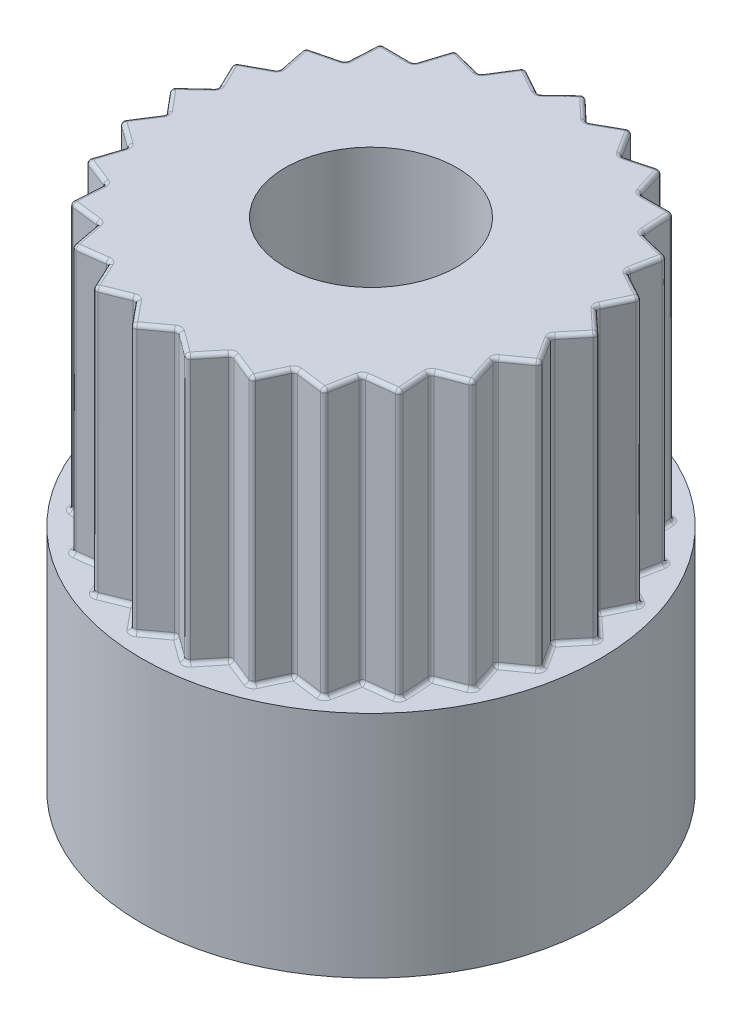
SolidWorks part; units mm, degrees
material "ABS"
ref_plane "Front Plane" through (0, 0, 0) normal (0, 0, 1) x (1, 0, 0)
ref_plane "Top Plane" through (0, 0, 0) normal (0, 1, 0) x (1, 0, 0)
ref_plane "Right Plane" through (0, 0, 0) normal (1, 0, 0) x (0, 0, -1)
sketch "Sketch1" plane through (0, 0, 0) normal (0, 1, 0) x (1, 0, 0)
  circle A0 centre (0, 0) radius 3
extrude "Boss-Extrude1" add sketch "Sketch1" along normal blind 3
sketch "Sketch2" plane through (0, 3, 0) normal (0, 1, 0) x (1, 0, 0)
  circle A0 centre (0, 0) radius 2.8
  dimension "D1" = 5.6
extrude "Boss-Extrude2" add sketch "Sketch2" along normal blind 3.5
sketch "Sketch3" plane through (0, 6.5, 0) normal (0, 1, 0) x (1, 0, 0)
  line L0 (0, 0) -> (0, 2.8) construction
  line L1 (0, 0) -> (0.3509, 2.7779) construction
  line L2 (0, 0) -> (-0.3509, 2.7779) construction
  line L3 (0, 2.8) -> (-0.3158, 2.5)
  line L4 (0, 2.8) -> (0.3158, 2.5)
  line L5 (0.6963, 2.712) -> (0.3158, 2.5)
  line L6 (0.6963, 2.712) -> (0.9276, 2.3429)
  line L7 (0, 0) -> (0.6963, 2.712) construction
  line L8 (1.3489, 2.4537) -> (0.9276, 2.3429)
  line L9 (1.3489, 2.4537) -> (1.4811, 2.0386)
  line L10 (0, 0) -> (1.3489, 2.4537) construction
  line L11 (1.9167, 2.0411) -> (1.4811, 2.0386)
  line L12 (1.9167, 2.0411) -> (1.9416, 1.6062)
  line L13 (0, 0) -> (1.9167, 2.0411) construction
  line L14 (2.3641, 1.5003) -> (1.9416, 1.6062)
  line L15 (2.3641, 1.5003) -> (2.28, 1.0729)
  line L16 (0, 0) -> (2.3641, 1.5003) construction
  line L17 (2.663, 0.8652) -> (2.28, 1.0729)
  line L18 (2.663, 0.8652) -> (2.4752, 0.4722)
  line L19 (0, 0) -> (2.663, 0.8652) construction
  line L20 (2.7945, 0.1758) -> (2.4752, 0.4722)
  line L21 (2.7945, 0.1758) -> (2.5149, -0.1582)
  line L22 (0, 0) -> (2.7945, 0.1758) construction
  line L23 (2.7504, -0.5247) -> (2.5149, -0.1582)
  line L24 (2.7504, -0.5247) -> (2.3965, -0.7787)
  line L25 (0, 0) -> (2.7504, -0.5247) construction
  line L26 (2.5335, -1.1922) -> (2.3965, -0.7787)
  line L27 (2.5335, -1.1922) -> (2.1276, -1.3502)
  line L28 (0, 0) -> (2.5335, -1.1922) construction
  line L29 (2.1574, -1.7848) -> (2.1276, -1.3502)
  line L30 (2.1574, -1.7848) -> (1.725, -1.8369)
  line L31 (0, 0) -> (2.1574, -1.7848) construction
  line L32 (1.6458, -2.2652) -> (1.725, -1.8369)
  line L33 (1.6458, -2.2652) -> (1.214, -2.2082)
  line L34 (0, 0) -> (1.6458, -2.2652) construction
  line L35 (1.0307, -2.6034) -> (1.214, -2.2082)
  line L36 (1.0307, -2.6034) -> (0.6267, -2.4407)
  line L37 (0, 0) -> (1.0307, -2.6034) construction
  line L38 (0.3509, -2.7779) -> (0.6267, -2.4407)
  line L39 (0.3509, -2.7779) -> (0, -2.5199)
  line L40 (0, 0) -> (0.3509, -2.7779) construction
  line L41 (-0.3509, -2.7779) -> (0, -2.5199)
  line L42 (-0.3509, -2.7779) -> (-0.6267, -2.4407)
  line L43 (0, 0) -> (-0.3509, -2.7779) construction
  line L44 (-1.0307, -2.6034) -> (-0.6267, -2.4407)
  line L45 (-1.0307, -2.6034) -> (-1.214, -2.2082)
  line L46 (0, 0) -> (-1.0307, -2.6034) construction
  line L47 (-1.6458, -2.2652) -> (-1.214, -2.2082)
  line L48 (-1.6458, -2.2652) -> (-1.725, -1.8369)
  line L49 (0, 0) -> (-1.6458, -2.2652) construction
  line L50 (-2.1574, -1.7848) -> (-1.725, -1.8369)
  line L51 (-2.1574, -1.7848) -> (-2.1276, -1.3502)
  line L52 (0, 0) -> (-2.1574, -1.7848) construction
  line L53 (-2.5335, -1.1922) -> (-2.1276, -1.3502)
  line L54 (-2.5335, -1.1922) -> (-2.3965, -0.7787)
  line L55 (0, 0) -> (-2.5335, -1.1922) construction
  line L56 (-2.7504, -0.5247) -> (-2.3965, -0.7787)
  line L57 (-2.7504, -0.5247) -> (-2.5149, -0.1582)
  line L58 (0, 0) -> (-2.7504, -0.5247) construction
  line L59 (-2.7945, 0.1758) -> (-2.5149, -0.1582)
  line L60 (-2.7945, 0.1758) -> (-2.4752, 0.4722)
  line L61 (0, 0) -> (-2.7945, 0.1758) construction
  line L62 (-2.663, 0.8652) -> (-2.4752, 0.4722)
  line L63 (-2.663, 0.8652) -> (-2.28, 1.0729)
  line L64 (0, 0) -> (-2.663, 0.8652) construction
  line L65 (-2.3641, 1.5003) -> (-2.28, 1.0729)
  line L66 (-2.3641, 1.5003) -> (-1.9416, 1.6062)
  line L67 (0, 0) -> (-2.3641, 1.5003) construction
  line L68 (-1.9167, 2.0411) -> (-1.9416, 1.6062)
  line L69 (-1.9167, 2.0411) -> (-1.4811, 2.0386)
  line L70 (0, 0) -> (-1.9167, 2.0411) construction
  line L71 (-1.3489, 2.4537) -> (-1.4811, 2.0386)
  line L72 (-1.3489, 2.4537) -> (-0.9276, 2.3429)
  line L73 (0, 0) -> (-1.3489, 2.4537) construction
  line L74 (-0.6963, 2.712) -> (-0.9276, 2.3429)
  line L75 (-0.6963, 2.712) -> (-0.3158, 2.5)
  line L76 (0, 0) -> (-0.6963, 2.712) construction
  circle A0 centre (0, 0) radius 2.8 construction
  circle A1 centre (0, 0) radius 2.8 construction
  circle A2 centre (0, 0) radius 3.6646
  point P87 (0, 0)
  dimension "D1" = 14.4
  dimension "D3" = 25
extrude "Cut-Extrude2" cut sketch "Sketch3" against normal blind 3.5
sketch "Sketch4" plane through (0, 6.5, 0) normal (0, 1, 0) x (1, 0, 0)
  circle A0 centre (0, 0) radius 1.125
  dimension "D1" = 2.25
extrude "Cut-Extrude3" cut sketch "Sketch4" against normal blind 5.5
fillet "Fillet2" radius 0.05 150 edges at (-2.6349, 6.5, -0.324) (-2.4715, 6.5, -0.9691) (-2.4715, 3, -0.9691) (-2.6327, 6.5, 0.3414) (-2.6349, 3, -0.324) (-2.465, 6.5, 0.9854) (-2.6327, 3, 0.3414) (-2.1425, 6.5, 1.5675) (-2.465, 3, 0.9854) (-1.6854, 6.5, 2.0511) (-2.1425, 3, 1.5675) (-1.1224, 6.5, 2.4058) (-1.6854, 3, 2.0511) (-0.4888, 6.5, 2.6093) (-1.1224, 3, 2.4058) (0.1755, 6.5, 2.6489) (-0.4888, 3, 2.6093) (0.8287, 6.5, 2.522) (0.1755, 3, 2.6489) (1.4299, 6.5, 2.2367) (0.8287, 3, 2.522) (1.9412, 6.5, 1.8108) (1.4299, 3, 2.2367) (2.3306, 6.5, 1.2712) (1.9412, 3, 1.8108) (2.5735, 6.5, 0.6517) (2.3306, 3, 1.2712) (2.6547, 6.5, -0.0088) (2.5735, 3, 0.6517) (2.5691, 6.5, -0.6687) (2.6547, 3, -0.0088) (2.3221, 6.5, -1.2866) (2.5691, 3, -0.6687) (1.9292, 6.5, -1.8237) (2.3221, 3, -1.2866) (1.415, 6.5, -2.2461) (1.9292, 3, -1.8237) (0.812, 6.5, -2.5275) (1.415, 3, -2.2461) (0.1579, 6.5, -2.65) (0.812, 3, -2.5275) (-0.5061, 6.5, -2.606) (0.1579, 3, -2.65) (-1.1383, 6.5, -2.3983) (-0.5061, 3, -2.606) (-1.6989, 6.5, -2.0399) (-1.1383, 3, -2.3983) (-1.6989, 3, -2.0399) (-2.4752, 4.75, -0.4722) (-2.5691, 6.5, -0.6687) (-2.5691, 3, -0.6687) (-2.663, 4.75, -0.8652) (-2.5149, 4.75, 0.1582) (-2.6547, 6.5, -0.0088) (-2.6547, 3, -0.0088) (-2.7945, 4.75, -0.1758) (-2.3965, 4.75, 0.7787) (-2.5735, 6.5, 0.6517) (-2.5735, 3, 0.6517) (-2.7504, 4.75, 0.5247) (-2.1276, 4.75, 1.3502) (-2.3306, 6.5, 1.2712) (-2.3306, 3, 1.2712) (-2.5335, 4.75, 1.1922) (-1.725, 4.75, 1.8369) (-1.9412, 6.5, 1.8108) (-1.9412, 3, 1.8108) (-2.1574, 4.75, 1.7848) (-1.214, 4.75, 2.2082) (-1.4299, 6.5, 2.2367) (-1.4299, 3, 2.2367) (-1.6458, 4.75, 2.2652) (-0.6267, 4.75, 2.4407) (-0.8287, 6.5, 2.522) (-0.8287, 3, 2.522) (-1.0307, 4.75, 2.6034) (0, 4.75, 2.5199) (-0.1755, 6.5, 2.6489) (-0.1755, 3, 2.6489) (-0.3509, 4.75, 2.7779) (0.6267, 4.75, 2.4407) (0.4888, 6.5, 2.6093) (0.4888, 3, 2.6093) (0.3509, 4.75, 2.7779) (1.214, 4.75, 2.2082) (1.1224, 6.5, 2.4058) (1.1224, 3, 2.4058) (1.0307, 4.75, 2.6034) (1.725, 4.75, 1.8369) (1.6854, 6.5, 2.0511) (1.6854, 3, 2.0511) (1.6458, 4.75, 2.2652) (2.1276, 4.75, 1.3502) (2.1425, 6.5, 1.5675) (2.1425, 3, 1.5675) (2.1574, 4.75, 1.7848) (2.3965, 4.75, 0.7787) (2.465, 6.5, 0.9854) (2.465, 3, 0.9854) (2.5335, 4.75, 1.1922) (2.5149, 4.75, 0.1582) (2.6327, 6.5, 0.3414) (2.6327, 3, 0.3414) (2.7504, 4.75, 0.5247) (2.4752, 4.75, -0.4722) (2.6349, 6.5, -0.324) (2.6349, 3, -0.324) (2.7945, 4.75, -0.1758) (2.28, 4.75, -1.0729) (2.4715, 6.5, -0.9691) (2.4715, 3, -0.9691) (2.663, 4.75, -0.8652) (1.9416, 4.75, -1.6062) (2.1529, 6.5, -1.5533) (2.1529, 3, -1.5533) (2.3641, 4.75, -1.5003) (1.4811, 4.75, -2.0386) (1.6989, 6.5, -2.0399) (1.6989, 3, -2.0399) (1.9167, 4.75, -2.0411) (0.9276, 4.75, -2.3429) (1.1383, 6.5, -2.3983) (1.1383, 3, -2.3983) (1.3489, 4.75, -2.4537) (0.3158, 4.75, -2.5) (0.5061, 6.5, -2.606) (0.5061, 3, -2.606) (0.6963, 4.75, -2.712) (-0.3158, 4.75, -2.5) (-0.1579, 6.5, -2.65) (-0.1579, 3, -2.65) (0, 4.75, -2.8) (-0.9276, 4.75, -2.3429) (-0.812, 6.5, -2.5275) (-0.812, 3, -2.5275) (-0.6963, 4.75, -2.712) (-1.4811, 4.75, -2.0386) (-1.415, 6.5, -2.2461) (-1.415, 3, -2.2461) (-1.3489, 4.75, -2.4537) (-1.9292, 6.5, -1.8237) (-1.9292, 3, -1.8237) (-1.9167, 4.75, -2.0411) (-2.1529, 6.5, -1.5533) (-2.1529, 3, -1.5533) (-1.9416, 4.75, -1.6062) (-2.28, 4.75, -1.0729) (-2.3221, 6.5, -1.2866) (-2.3221, 3, -1.2866) (-2.3641, 4.75, -1.5003)
